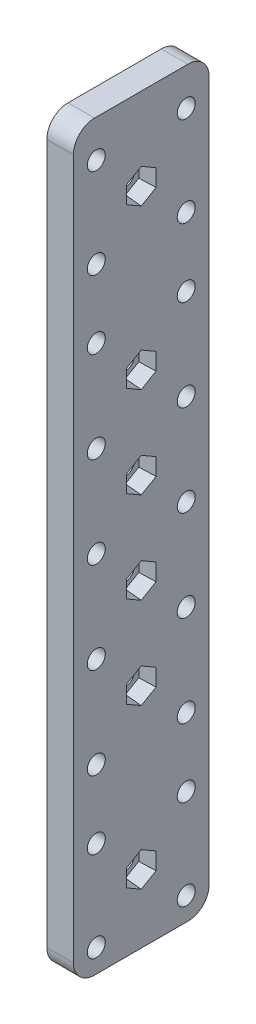
SolidWorks part; units mm, degrees
ref_plane "Plan de face" through (0, 0, 0) normal (0, 0, 1) x (1, 0, 0)
ref_plane "Plan de dessus" through (0, 0, 0) normal (0, 1, 0) x (1, 0, 0)
ref_plane "Plan de droite" through (0, 0, 0) normal (1, 0, 0) x (0, 0, -1)
sketch "Esquisse2" plane through (0, 0, 0) normal (1, 0, 0) x (0, 0, -1)
  line L0 (-12.8, -125.0284) -> (-21.2853, -133.5136) construction
  line L1 (-12.8, -125.0284) -> (-12.8, -134.7242) construction
  line L2 (-12.8, -95.0284) -> (-21.2853, -103.6294) construction
  line L3 (-12.8, -137.8939) -> (-12.8, 2.1061) construction
  line L4 (-25.6, -133.8939) -> (-25.6, -1.8939)
  line L5 (-21.6, 2.1061) -> (-4.0046, 2.1061)
  line L6 (-12.8, -95.0284) -> (-22.9445, -95.0284) construction
  line L7 (-21.2853, -86.4273) -> (-4.3147, -86.4273) construction
  line L8 (-21.2853, -69.2253) -> (-4.3147, -69.2253) construction
  line L9 (-21.2853, -52.0232) -> (-4.3147, -52.0232) construction
  line L10 (-12.8, -13.4222) -> (-21.2853, -4.9369) construction
  line L11 (-12.8, -125.0284) -> (-17.4685, -125.0284) construction
  line L12 (-12.8, -13.4222) -> (-17.4685, -13.4222) construction
  line L13 (-12.8, 2.1061) -> (-34.3041, 2.1061) construction
  line L14 (-12.8, 2.1061) -> (12.7906, 2.1061) construction
  line L15 (-12.8, -137.8939) -> (-36.0071, -137.8939) construction
  line L16 (-12.8, -137.8939) -> (9.0017, -137.8939) construction
  line L17 (0, 11.7367) -> (0, -147.584) construction
  line L18 (-25.6, 11.7367) -> (-25.6, -147.584) construction
  line L19 (-0.0046, -1.8938) -> (-0.0001, -133.8938)
  line L20 (-4.0001, -137.8939) -> (-21.6, -137.8939)
  circle A0 centre (-12.8, -95.0284) radius 7.5 construction
  circle A1 centre (-21.2853, -103.6294) radius 1.7
  circle A2 centre (-4.3147, -103.6294) radius 1.7
  circle A3 centre (-4.3147, -86.4273) radius 1.7
  circle A4 centre (-21.2853, -86.4273) radius 1.7
  circle A5 centre (-21.2853, -133.5136) radius 1.7
  circle A6 centre (-12.8, -125.0284) radius 7.5 construction
  circle A7 centre (-4.3147, -133.5136) radius 1.7
  circle A8 centre (-4.3147, -69.2253) radius 1.7
  circle A9 centre (-21.2853, -69.2253) radius 1.7
  circle A10 centre (-12.8, -77.8263) radius 7.5 construction
  circle A11 centre (-4.3147, -52.0232) radius 1.7
  circle A12 centre (-21.2853, -52.0232) radius 1.7
  circle A13 centre (-12.8, -60.6243) radius 7.5 construction
  circle A14 centre (-4.3147, -34.8212) radius 1.7
  circle A15 centre (-21.2853, -34.8212) radius 1.7
  circle A16 centre (-12.8, -43.4222) radius 7.5 construction
  circle A17 centre (-12.8, -13.4222) radius 7.5 construction
  circle A18 centre (-21.2853, -4.9369) radius 1.7
  circle A19 centre (-4.3147, -4.9369) radius 1.7
  circle A20 centre (-4.3147, -116.5431) radius 1.7
  circle A21 centre (-21.2853, -116.5431) radius 1.7
  circle A22 centre (-4.3147, -21.9075) radius 1.7
  circle A23 centre (-21.2853, -21.9075) radius 1.7
  arc A24 (-25.6, -133.8939) -> (-21.6, -137.8939) centre (-21.6, -133.8939) ccw
  arc A25 (-0.0001, -133.8938) -> (-4.0001, -137.8939) centre (-4.0001, -133.8939) cw
  arc A26 (-4.0046, 2.1061) -> (-0.0046, -1.8938) centre (-4.0046, -1.8939) cw
  arc A27 (-25.6, -1.8939) -> (-21.6, 2.1061) centre (-21.6, -1.8939) cw
  circle A28 centre (-12.8, -13.4222) radius 1.7
  circle A29 centre (-12.8, -43.4222) radius 1.7
  circle A30 centre (-12.8, -60.6243) radius 1.7
  circle A31 centre (-12.8, -77.8263) radius 1.7
  circle A32 centre (-12.8, -95.0284) radius 1.7
  circle A33 centre (-12.8, -125.0284) radius 1.7
  point P68 (-25.6, -137.8939)
  point P71 (0, -137.8939)
  point P74 (-0.0047, 2.1061)
  point P77 (-25.6, 2.1061)
  dimension "D1" = 30
  dimension "D3" = 12.8
  dimension "D4" = 4
  dimension "D2" = 30
extrude "Boss.-Extru.1" add sketch "Esquisse2" along normal blind 5
sketch "Esquisse3" plane through (5, 0, 0) normal (1, 0, 0) x (0, 0, -1)
  line L1 (-12.8, -10.189) -> (-15.6, -11.8056)
  line L2 (-15.6, -11.8056) -> (-15.6, -15.0388)
  line L3 (-15.6, -15.0388) -> (-12.8, -16.6554)
  line L4 (-12.8, -16.6554) -> (-10, -15.0388)
  line L5 (-10, -15.0388) -> (-10, -11.8056)
  line L6 (-10, -11.8056) -> (-12.8, -10.189)
  line L7 (-12.8, -40.189) -> (-15.6, -41.8056)
  line L8 (-15.6, -41.8056) -> (-15.6, -45.0388)
  line L9 (-15.6, -45.0388) -> (-12.8, -46.6554)
  line L10 (-12.8, -46.6554) -> (-10, -45.0388)
  line L11 (-10, -45.0388) -> (-10, -41.8056)
  line L12 (-10, -41.8056) -> (-12.8, -40.189)
  line L13 (-12.8, -57.3911) -> (-15.6, -59.0077)
  line L14 (-15.6, -59.0077) -> (-15.6, -62.2408)
  line L15 (-15.6, -62.2408) -> (-12.8, -63.8574)
  line L16 (-12.8, -63.8574) -> (-10, -62.2408)
  line L17 (-10, -62.2408) -> (-10, -59.0077)
  line L18 (-10, -59.0077) -> (-12.8, -57.3911)
  line L19 (-12.8, -74.5931) -> (-15.6, -76.2097)
  line L20 (-15.6, -76.2097) -> (-15.6, -79.4429)
  line L21 (-15.6, -79.4429) -> (-12.8, -81.0595)
  line L22 (-12.8, -81.0595) -> (-10, -79.4429)
  line L23 (-10, -79.4429) -> (-10, -76.2097)
  line L24 (-10, -76.2097) -> (-12.8, -74.5931)
  line L25 (-12.8, -91.7952) -> (-15.6, -93.4118)
  line L26 (-15.6, -93.4118) -> (-15.6, -96.6449)
  line L27 (-15.6, -96.6449) -> (-12.8, -98.2615)
  line L28 (-12.8, -98.2615) -> (-10, -96.6449)
  line L29 (-10, -96.6449) -> (-10, -93.4118)
  line L30 (-10, -93.4118) -> (-12.8, -91.7952)
  line L31 (-12.8, -121.7952) -> (-15.6, -123.4118)
  line L32 (-15.6, -123.4118) -> (-15.6, -126.6449)
  line L33 (-15.6, -126.6449) -> (-12.8, -128.2615)
  line L34 (-12.8, -128.2615) -> (-10, -126.6449)
  line L35 (-10, -126.6449) -> (-10, -123.4118)
  line L36 (-10, -123.4118) -> (-12.8, -121.7952)
  circle A0 centre (-12.8, -13.4222) radius 2.8 construction
  circle A1 centre (-12.8, -43.4222) radius 2.8 construction
  circle A2 centre (-12.8, -60.6243) radius 2.8 construction
  circle A3 centre (-12.8, -77.8263) radius 2.8 construction
  circle A4 centre (-12.8, -95.0284) radius 2.8 construction
  circle A5 centre (-12.8, -125.0284) radius 2.8 construction
extrude "Enlèv. mat.-Extru.1" cut sketch "Esquisse3" against normal blind 3 draft 5
